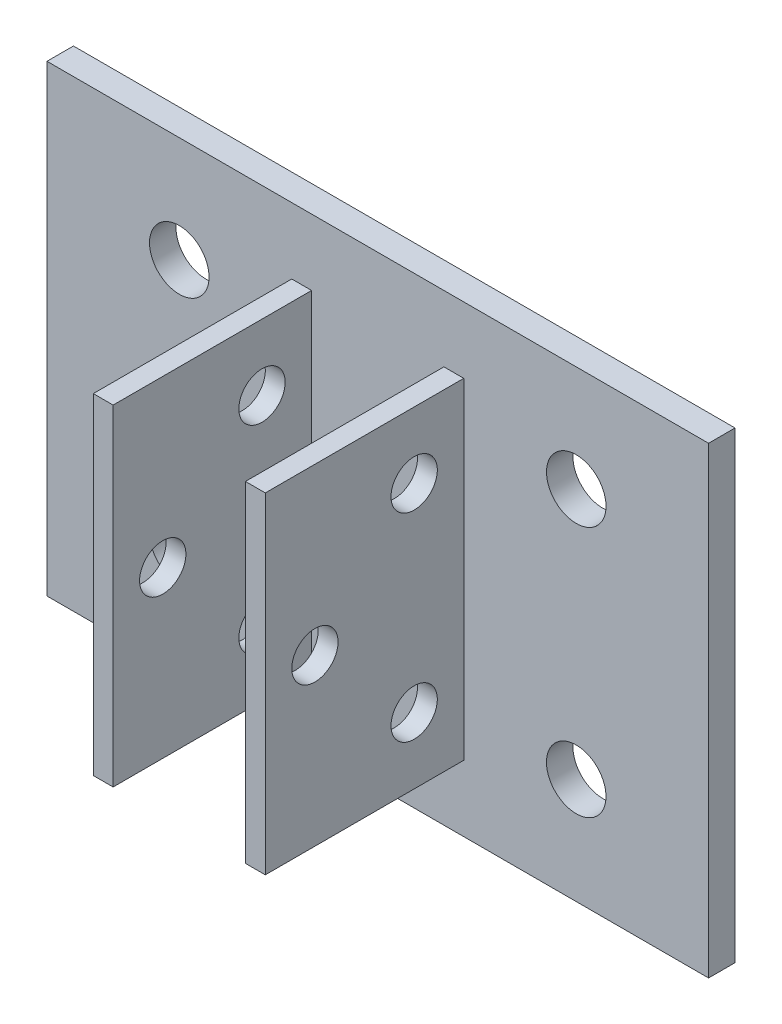
SolidWorks part; units mm, degrees
ref_plane "Front" through (0, 0, 0) normal (0, 0, 1) x (1, 0, 0)
ref_plane "Top" through (0, 0, 0) normal (0, 1, 0) x (1, 0, 0)
ref_plane "Right" through (0, 0, 0) normal (1, 0, 0) x (0, 0, -1)
sketch "Sketch2" plane through (0, 0, 0) normal (0, 0, 1) x (1, 0, 0)
  line L0 (0, 17.5) -> (0, -17.5) construction
  line L1 (-25, -17.5) -> (25, -17.5)
  line L2 (-25, -17.5) -> (-25, 17.5)
  line L3 (-25, 17.5) -> (25, 17.5)
  line L4 (25, -17.5) -> (25, 17.5)
  line L5 (-25, -17.5) -> (25, 17.5) construction
  line L6 (-25, 17.5) -> (25, -17.5) construction
  line L7 (-25, 0) -> (25, 0) construction
  circle A0 centre (15, 9.5) radius 2.25
  circle A1 centre (-15, 9.5) radius 2.25
  circle A2 centre (-15, -9.5) radius 2.25
  circle A3 centre (15, -9.5) radius 2.25
  point P0 (0, 0)
  dimension "D3" = 4.5
  dimension "D1" = 35
  dimension "D2" = 50
  dimension "D4" = 10
  dimension "D5" = 8
extrude "Boss-Extrude1" add sketch "Sketch2" along normal blind 2
sketch "Sketch3" plane through (0, 0, 2) normal (0, 0, 1) x (1, 0, 0)
  line L0 (0, 17.5) -> (0, -17.5) construction
  line L1 (25, 17.5) -> (-25, 17.5) construction
  line L2 (-25, -17.5) -> (25, -17.5) construction
  line L3 (5, 12.5) -> (5, -12.5)
  line L4 (-6.5, -12.5) -> (6.5, -12.5)
  line L5 (-6.5, -12.5) -> (-6.5, 12.5)
  line L6 (-6.5, 12.5) -> (6.5, 12.5)
  line L7 (6.5, -12.5) -> (6.5, 12.5)
  line L8 (-6.5, -12.5) -> (6.5, 12.5) construction
  line L9 (-6.5, 12.5) -> (6.5, -12.5) construction
  line L10 (-5, 12.5) -> (-5, -12.5)
  point P6 (0, 0)
  dimension "D1" = 13
  dimension "D2" = 10
  dimension "D3" = 25
extrude "Boss-Extrude2" add sketch "Sketch3" along normal blind 15 contours L10 L6 L5 L4 | L4 L7 L6 L3
sketch "Sketch4" plane through (-6.5, 0, 0) normal (-1, 0, 0) x (0, 0, 1)
  line L0 (9.5, 12.5) -> (9.5, -12.5) construction
  line L1 (17, 12.5) -> (2, 12.5) construction
  line L2 (17, -12.5) -> (2, -12.5) construction
  circle A0 centre (13.25, 0) radius 1.75
  circle A1 centre (5.75, 7.5) radius 1.75
  circle A2 centre (5.75, -7.5) radius 1.75
  dimension "D1" = 3.5
  dimension "D2" = 3.75
  dimension "D3" = 3.75
  dimension "D4" = 5
  dimension "D5" = 5
  dimension "D6" = 3.75
extrude "Cut-Extrude1" cut sketch "Sketch4" against normal through all contours A2 | A1 | A0
